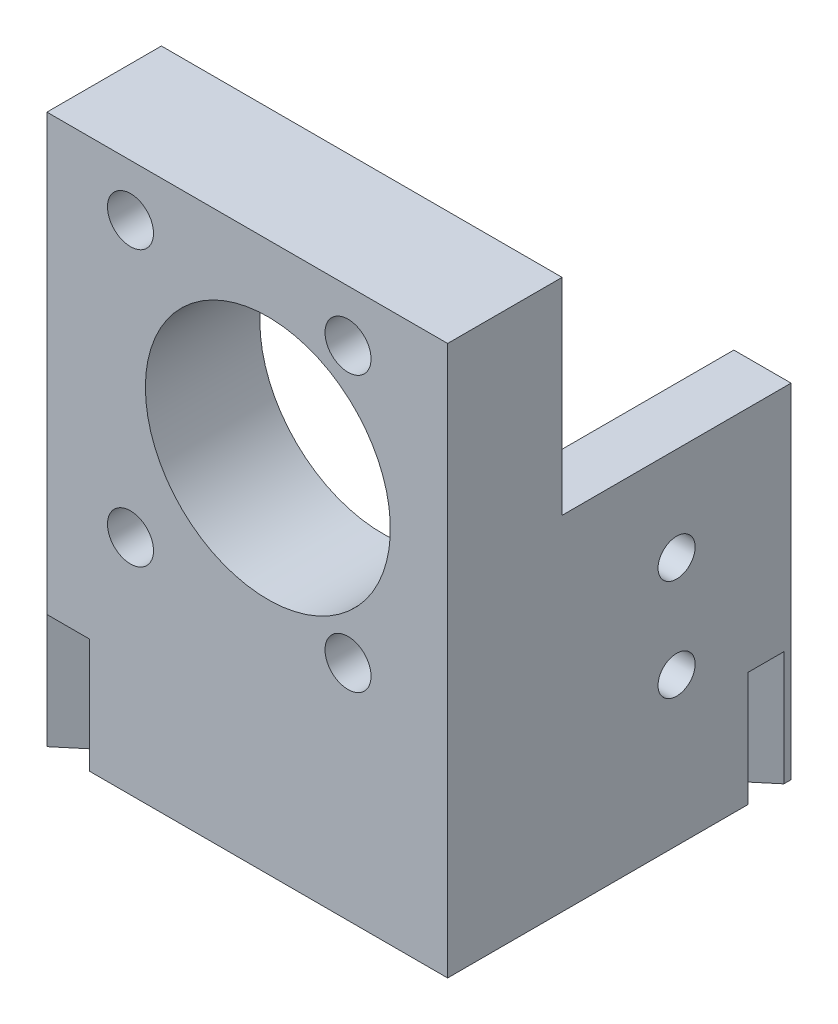
SolidWorks part; units mm, degrees
material "6061 Alloy"
ref_plane "Front Plane" through (0, 0, 0) normal (0, 0, 1) x (1, 0, 0)
ref_plane "Top Plane" through (0, 0, 0) normal (0, 1, 0) x (1, 0, 0)
ref_plane "Right Plane" through (0, 0, 0) normal (1, 0, 0) x (0, 0, -1)
sketch "Sketch1" plane through (0, 0, 0) normal (0, 1, 0) x (1, 0, 0)
  line L0 (-44.45, 12.7) -> (-44.45, 0)
  line L1 (-44.45, 0) -> (0, 0)
  line L2 (0, 0) -> (0, 38.1)
  line L3 (0, 38.1) -> (-6.35, 38.1)
  line L4 (-6.35, 38.1) -> (-6.35, 12.7)
  line L5 (-6.35, 12.7) -> (-44.45, 12.7)
  dimension "D1" = 12.7
  dimension "D2" = 38.1
  dimension "D3" = 6.35
  dimension "D4" = 25.4
extrude "Boss-Extrude1" add sketch "Sketch1" along normal blind 60.96
sketch "Sketch4" plane through (-6.35, 0, 0) normal (-1, 0, 0) x (0, 0, 1)
  line L0 (-25.4, 0) -> (-25.4, 60.96) construction
  line L1 (-38.1, 0) -> (-12.7, 0) construction
  line L2 (-38.1, 60.96) -> (-12.7, 60.96) construction
  circle A0 centre (-25.4, 16.4338) radius 2.0574
  circle A1 centre (-25.4, 27.686) radius 2.0574
  dimension "D1" = 11.2522
  dimension "D2" = 4.1148
  dimension "D3" = 27.686
extrude "Cut-Extrude3" cut sketch "Sketch4" against normal through all
sketch "Sketch3" plane through (0, 0, -12.7) normal (0, 0, -1) x (-1, 0, 0)
  line L0 (0, 60.96) -> (0, 0) construction
  line L1 (44.45, 39.9796) -> (19.939, 39.9796) construction
  line L2 (19.939, 39.9796) -> (-49980.061, 39.9796) construction
  line L3 (6.35, 25.6286) -> (6.35, 29.7434) construction
  line L4 (6.35, 25.6286) -> (6.35, 29.7434) construction
  line L5 (44.45, 60.96) -> (44.45, 0) construction
  line L6 (6.35, 60.96) -> (6.35, 0) construction
  circle A0 centre (19.939, 39.9796) radius 13.589
  circle A1 centre (35.179, 55.2196) radius 2.54
  circle A2 centre (11.049, 55.2196) radius 2.54
  circle A3 centre (11.049, 24.7396) radius 2.54
  circle A4 centre (35.179, 24.7396) radius 2.54
  point P4 (6.35, 27.686)
  point P21 (19.939, 39.9796)
  dimension "D1" = 15.24
  dimension "D5" = 5.08
  dimension "D2" = 12.2936
  dimension "D3" = 19.939
  dimension "D4" = 15.24
  dimension "D6" = 8.89
  dimension "D7" = 15.24
extrude "Cut-Extrude2" cut sketch "Sketch3" against normal through all
sketch "Sketch6" plane through (0, 0, 0) normal (0, -1, 0) x (1, 0, 0)
  line L0 (-47.8911, 6.8663) -> (10.4815, -42.1141)
  line L1 (10.4815, -42.1141) -> (8.5223, -44.449)
  line L2 (8.5223, -44.449) -> (-49.8503, 4.5314)
  line L3 (-49.8503, 4.5314) -> (-47.8911, 6.8663)
  line L4 (-44.45, 0) -> (0, 0) construction
  dimension "D1" = 3.048
  dimension "D2" = 40
  dimension "D3" = 76.2
extrude "Cut-Extrude4" cut sketch "Sketch6" against normal blind 12.7
sketch "Sketch7" plane through (-16.4065, 0, -19.5524) normal (-0.6428, 0, -0.766) x (-0.766, 0, 0.6428)
  line L0 (-24.4902, 25.7013) -> (34.0507, 25.7013) construction
  line L1 (-24.4902, 60.96) -> (-24.4902, 0) construction
  line L2 (34.0507, 60.96) -> (34.0507, 12.7) construction
  line L3 (4.7802, 60.96) -> (4.7802, 25.7013) construction
  line L4 (-3.299, 60.96) -> (25.8873, 60.96) construction
  line L5 (4.7802, 25.7013) -> (4.7802, 0) construction
  line L6 (-3.299, 0) -> (10.6605, 0) construction
  point P7 (4.7802, 25.7013)
ref_plane "Plane1" through (-21.3045, 0, -25.3897) normal (-0.6428, 0, -0.766) x (-0.766, 0, 0.6428)
sketch "Sketch9" plane through (-21.3045, 0, -25.3897) normal (-0.6428, 0, -0.766) x (-0.766, 0, 0.6428)
  line L0 (4.7802, 60.96) -> (4.7802, 25.7013) construction
  line L1 (4.7802, 25.7013) -> (4.7802, 0) construction
  line L2 (4.7802, 60.96) -> (4.7802, 25.7013) construction
  line L3 (4.7802, 25.7013) -> (4.7802, 0) construction
ref_plane "Center plane" through (-3.6619, 0, 3.0727) normal (-0.766, 0, 0.6428) x (0.6428, 0, 0.766)
sketch "Sketch10" plane through (0, 60.96, 0) normal (0, 1, 0) x (1, 0, 0)
  line L1 (-6.35, 12.7) -> (0, 12.7)
  line L2 (-6.35, 12.7) -> (-6.35, 38.1)
  line L3 (-6.35, 38.1) -> (0, 38.1)
  line L4 (0, 12.7) -> (0, 38.1)
extrude "Cut-Extrude5" cut sketch "Sketch10" against normal blind 22.86
hole_wizard "1/4-20 Tapped Hole1" positions "Sketch12" profile "Sketch11" tap size "1/4-20" standard "ANSI Inch"
sketch "Sketch12" plane through (0, 0, 0) normal (0, 0, 1) x (1, 0, 0)
  point P0 (-35.179, 55.2196)
  point P3 (-11.049, 55.2196)
  point P6 (-35.179, 24.7396)
  point P9 (-11.049, 24.7396)
sketch "Sketch11" plane through (-35.179, 55.2196, 0) normal (1, 0, 0) x (0, -1, 0)
  line L0 (0, 0) -> (0, 18.0438)
  line L1 (0, 18.0438) -> (2.5527, 16.51)
  line L2 (2.5527, 16.51) -> (2.5527, 0)
  line L5 (2.5527, 0) -> (0, 0)
  line L10 (0, 18.0438) -> (-2.5527, 16.51) construction
  line L11 (0, -6.35) -> (0, 107.95) construction
  dimension "Tap Drill Dia." = 5.1054
  dimension "Tap Drill Depth" = 16.51
  dimension "Drill Angle" = 118
cosmetic thread "Hole Thread1" parameters "D1"=12.7, "D2"=6.35
cosmetic thread "Hole Thread2" parameters "D1"=12.7, "D2"=6.35
cosmetic thread "Hole Thread3" parameters "D1"=12.7, "D2"=6.35
cosmetic thread "Hole Thread4" parameters "D1"=12.7, "D2"=6.35
